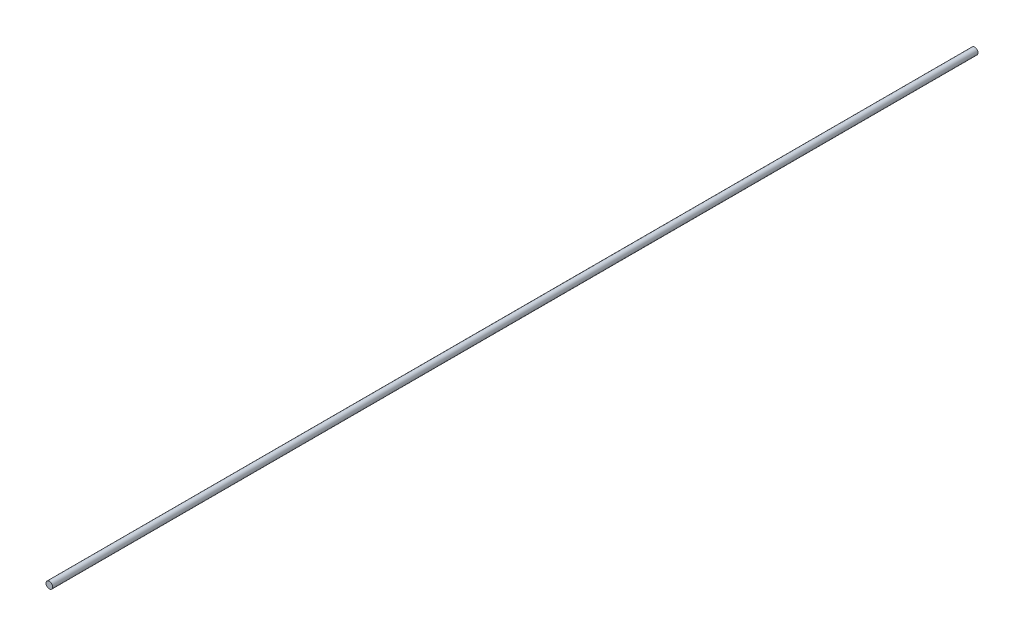
SolidWorks part; units mm, degrees
material "Cast Alloy Steel"
ref_plane "Front Plane" through (0, 0, 0) normal (0, 0, 1) x (1, 0, 0)
ref_plane "Top Plane" through (0, 0, 0) normal (0, 1, 0) x (1, 0, 0)
ref_plane "Right Plane" through (0, 0, 0) normal (1, 0, 0) x (0, 0, -1)
sketch "Sketch1" plane through (0, 0, 0) normal (0, 0, 1) x (1, 0, 0)
  circle A0 centre (0, 0) radius 1.15
  dimension "D1" = 2.3
extrude "Boss-Extrude1" add sketch "Sketch1" along normal blind 319
